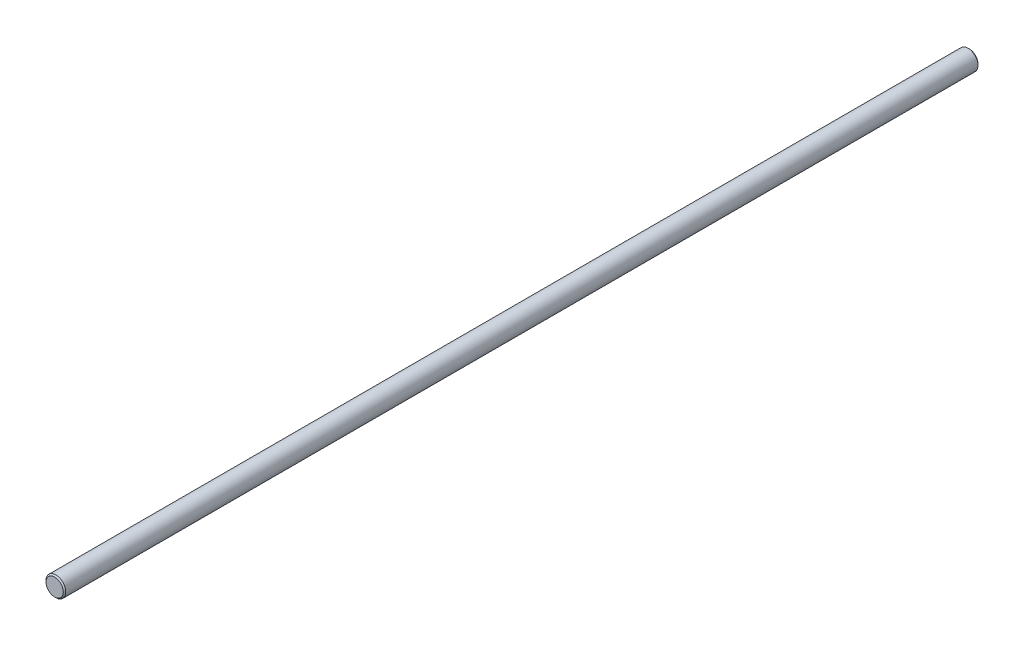
SolidWorks part; units mm, degrees
material "AISI 304"
ref_plane "Front Plane" through (0, 0, 0) normal (0, 0, 1) x (1, 0, 0)
ref_plane "Top Plane" through (0, 0, 0) normal (0, 1, 0) x (1, 0, 0)
ref_plane "Right Plane" through (0, 0, 0) normal (1, 0, 0) x (0, 0, -1)
sketch "Sketch1" plane through (0, 0, 0) normal (0, 0, 1) x (1, 0, 0)
  circle A0 centre (0, 0) radius 4
  dimension "D1" = 8
extrude "Boss-Extrude1" add sketch "Sketch1" against normal blind 370
chamfer "Chamfer1" distance 0.5 angle 45 2 edges at (4, 0, -370) (4, 0, 0)
